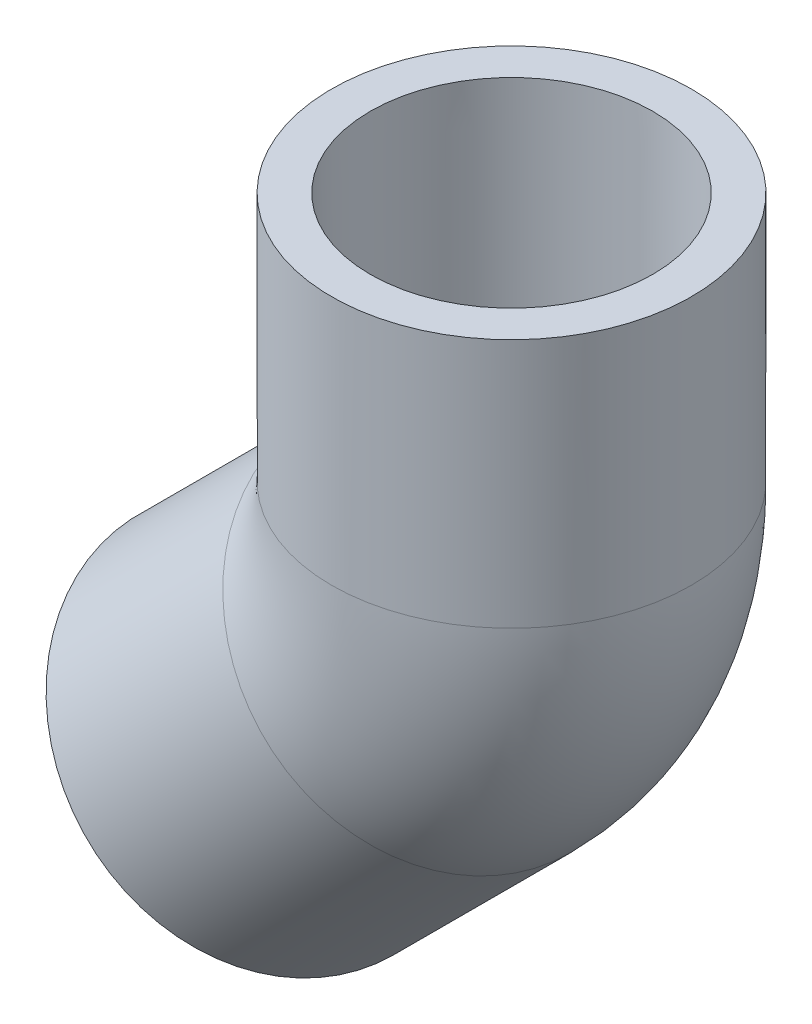
SolidWorks part; units mm, degrees
ref_plane "Front Plane" through (0, 0, 0) normal (0, 0, 1) x (1, 0, 0)
ref_plane "Top Plane" through (0, 0, 0) normal (0, 1, 0) x (1, 0, 0)
ref_plane "Right Plane" through (0, 0, 0) normal (1, 0, 0) x (0, 0, -1)
sketch "Sketch0" plane through (0, 0, 0) normal (0, 0, 1) x (1, 0, 0)
  line L0 (-18.6789, -18.6789) -> (0, 0) construction
  line L1 (0, 0) -> (0, 26.416) construction
  line L2 (-5.2085, -5.2085) -> (0, 0) construction
  line L3 (0, 0) -> (0, 7.366) construction
  line L4 (-28.3776, -8.9803) -> (-8.9803, -28.3776) construction
  line L5 (-12.716, 2.2989) -> (-26.2942, -11.0637) construction
  line L6 (-12.716, 2.2989) -> (2.2989, -12.716) construction
  line L7 (2.2989, -12.716) -> (-11.0637, -26.2942) construction
  line L8 (-26.2942, -11.0637) -> (-11.0637, -26.2942) construction
  line L9 (-13.716, 26.416) -> (13.716, 26.416) construction
  line L10 (-10.7696, 26.416) -> (10.7696, 26.416) construction
  line L11 (10.7696, 26.416) -> (10.6172, 7.366) construction
  line L12 (10.6172, 7.366) -> (-10.6172, 7.366) construction
  line L13 (-10.6172, 7.366) -> (-10.7696, 26.416) construction
  line L14 (-10.7943, 0.3772) -> (0.3772, -10.7943) construction
  line L18 (-7.8994, 7.366) -> (7.8994, 7.366) construction
  dimension "D1" = 45
  dimension "H" = 26.416
  dimension "J" = 7.366
  dimension "M" = 27.432
  dimension "OD A" = 21.5392
  dimension "OD B" = 21.2344
  dimension "ID" = 15.7988
sketch "Sketch1" plane through (0, 0, 0) normal (0, 0, 1) x (1, 0, 0)
  line L0 (-18.6789, -18.6789) -> (0, 0) construction
  line L1 (-18.6789, -18.6789) -> (0, 0) construction
  line L3 (-8.9803, -28.3776) -> (4.4901, -14.9072)
  line L4 (-8.9803, -28.3776) -> (-11.0637, -26.2942)
  line L5 (-11.0637, -26.2942) -> (2.2989, -12.716)
  line L6 (4.4901, -14.9072) -> (2.2989, -12.716)
revolve "Revolve1" add sketch "Sketch1" angle 360 about L1
sketch "Sketch2" plane through (0, 0, 0) normal (0, 0, 1) x (1, 0, 0)
  line L0 (10.7696, 26.416) -> (10.6172, 7.366)
  line L1 (10.6172, 7.366) -> (13.716, 7.366)
  line L2 (13.716, 7.366) -> (13.716, 26.416)
  line L3 (13.716, 26.416) -> (10.7696, 26.416)
  line L4 (0, 0) -> (0, 26.416) construction
  line L5 (0, 0) -> (0, 26.416) construction
revolve "Revolve2" add sketch "Sketch2" angle 360 about L5
sketch "Sketch3" plane through (-5.2085, -5.2085, 0) normal (0.7071, 0.7071, 0) x (0, 0, -1)
  circle A0 centre (0, 0) radius 7.8994
  circle A1 centre (0, 0) radius 13.716
sketch "Sketch4" plane through (0, 0, 0) normal (0, 0, 1) x (1, 0, 0)
  line L0 (-18.6789, -18.6789) -> (0, 0) construction
  line L1 (0, 0) -> (0, 26.416) construction
  line L2 (-18.6789, -18.6789) -> (-5.2085, -5.2085) construction
  line L3 (0, 7.366) -> (0, 26.416) construction
  arc A0 (-5.2085, -5.2085) -> (0, 7.366) centre (-17.7831, 7.366) ccw
sweep "Sweep1" add profiles "Sketch3" path "Sketch4"
